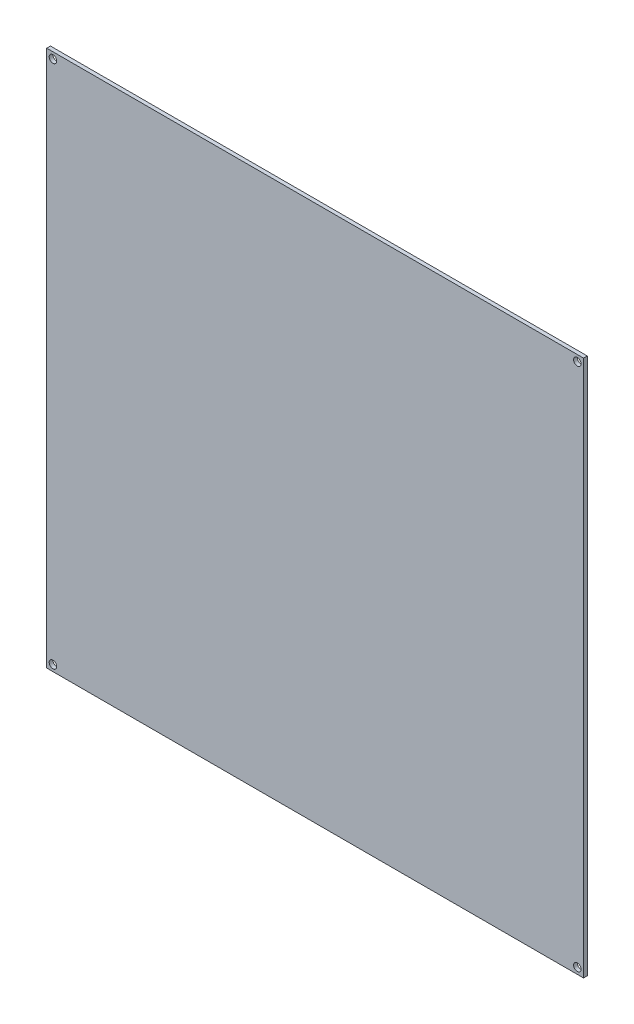
SolidWorks part; units mm, degrees
ref_plane "Plano frontal" through (0, 0, 0) normal (0, 0, 1) x (1, 0, 0)
ref_plane "Plano superior" through (0, 0, 0) normal (0, 1, 0) x (1, 0, 0)
ref_plane "Plano direito" through (0, 0, 0) normal (1, 0, 0) x (0, 0, -1)
sketch "Esboço1" plane through (0, 0, 0) normal (0, 0, 1) x (1, 0, 0)
  line L1 (-107.5, 107.5) -> (107.5, 107.5)
  line L2 (-107.5, 107.5) -> (-107.5, -107.5)
  line L3 (-107.5, -107.5) -> (107.5, -107.5)
  line L4 (107.5, 107.5) -> (107.5, -107.5)
  line L5 (-107.5, 107.5) -> (107.5, -107.5) construction
  line L6 (-107.5, -107.5) -> (107.5, 107.5) construction
  circle A0 centre (-105, 105) radius 1.5
  circle A1 centre (105, 105) radius 1.5
  circle A2 centre (105, -105) radius 1.5
  circle A3 centre (-105, -105) radius 1.5
  point P0 (0, 0)
  point P14 (0, 0)
  point P15 (0, 0)
  dimension "D3" = 3
  dimension "D1" = 215
  dimension "D2" = 215
  dimension "D4" = 210
extrude "Ressalto-extrusão1" add sketch "Esboço1" along normal blind 1.5
